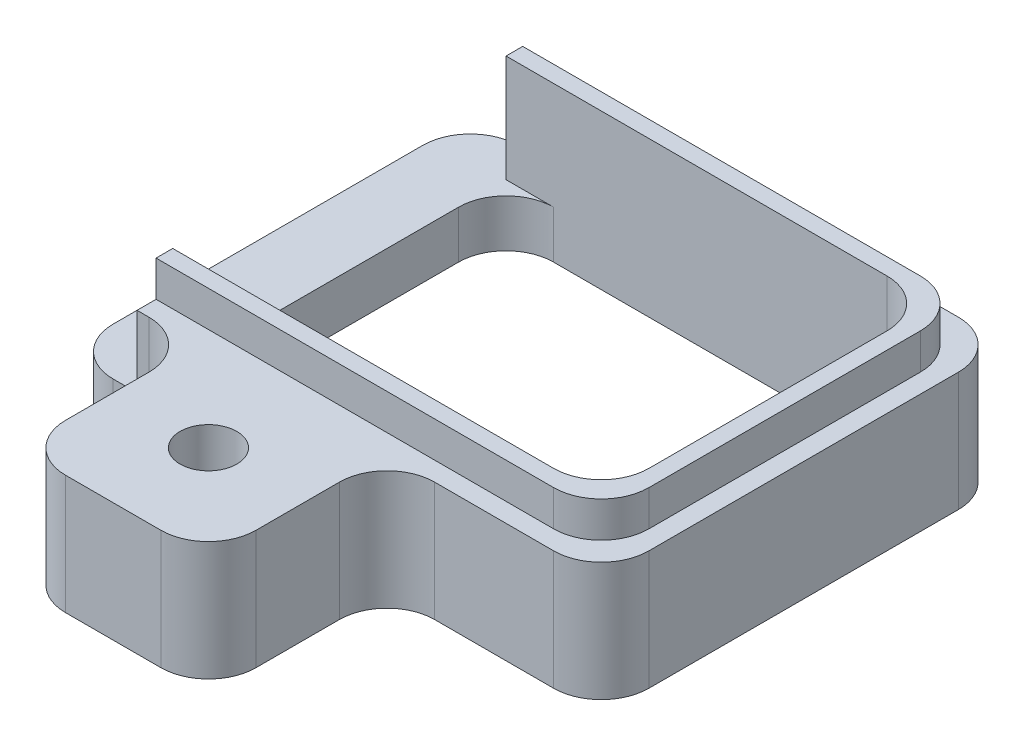
SolidWorks part; units mm, degrees
ref_plane "Front Plane" through (0, 0, 0) normal (0, 0, 1) x (1, 0, 0)
ref_plane "Top Plane" through (0, 0, 0) normal (0, 1, 0) x (1, 0, 0)
ref_plane "Right Plane" through (0, 0, 0) normal (1, 0, 0) x (0, 0, -1)
sketch "Sketch5" plane through (0, 0, 0) normal (0, 1, 0) x (1, 0, 0)
  line L1 (-5.625, -4.25) -> (5.625, -4.25)
  line L2 (-5.625, -4.25) -> (-5.625, 4.25)
  line L3 (-5.625, 4.25) -> (5.625, 4.25)
  line L4 (5.625, -4.25) -> (5.625, 4.25)
  line L5 (-5.625, -4.25) -> (5.625, 4.25) construction
  line L6 (-5.625, 4.25) -> (5.625, -4.25) construction
  point P0 (0, 0)
  dimension "D1" = 8.5
  dimension "D2" = 11.25
extrude "Extrude4" add sketch "Sketch5" along normal blind 2.5
sketch "Sketch19" plane through (0, 2.5, 0) normal (0, 1, 0) x (-1, 0, 0)
  line L0 (5.625, 4.25) -> (-5.625, 4.25) construction
  line L1 (5.625, -4.25) -> (4.125, -4.25)
  line L2 (5.625, -4.25) -> (5.625, 4.25)
  line L3 (5.625, 4.25) -> (4.125, 4.25)
  line L4 (4.125, -4.25) -> (4.125, 4.25)
  dimension "D1" = 1.5
extrude "Extrude12" cut sketch "Sketch19" against normal blind 1.5
sketch "Sketch21" plane through (0, 2.5, 0) normal (0, 1, 0) x (-1, 0, 0)
  line L0 (4.125, 4.25) -> (4.125, -4.25) construction
  line L1 (-4.875, -3.5) -> (4.125, -3.5)
  line L2 (-4.875, -3.5) -> (-4.875, 3.5)
  line L3 (-4.875, 3.5) -> (4.125, 3.5)
  line L4 (4.125, -3.5) -> (4.125, 3.5)
  line L5 (-5.625, -4.25) -> (4.125, -4.25) construction
  line L6 (-5.625, 4.25) -> (-5.625, -4.25) construction
  line L7 (4.125, 4.25) -> (-5.625, 4.25) construction
  dimension "D1" = 0.75
  dimension "D2" = 0.75
  dimension "D3" = 0.75
extrude "Extrude13" cut sketch "Sketch21" against normal through all
sketch "Sketch22" plane through (0, 0, 4.25) normal (0, 0, 1) x (1, 0, 0)
  line L0 (-4.125, 2.5) -> (5.625, 2.5) construction
  line L1 (-2.875, 2.5) -> (1.125, 2.5)
  line L2 (-2.875, 2.5) -> (-2.875, 0)
  line L3 (-2.875, 0) -> (1.125, 0)
  line L4 (1.125, 2.5) -> (1.125, 0)
  line L5 (5.625, 2.5) -> (5.625, 0) construction
  line L6 (-5.625, 0) -> (5.625, 0) construction
  point P8 (0, 0)
  dimension "D1" = 4
  dimension "D2" = 4.5
  dimension "D3" = 0
extrude "Extrude14" add sketch "Sketch22" along normal blind 3.75
sketch "Sketch24" plane through (0, 2.5, 0) normal (0, 1, 0) x (1, 0, 0)
  line L0 (-4.125, 3.85) -> (-4.125, 3.5)
  line L1 (-4.125, 3.5) -> (4.875, 3.5)
  line L2 (4.875, 3.5) -> (4.875, -3.5)
  line L3 (4.875, -3.5) -> (-4.125, -3.5)
  line L4 (-4.125, -3.5) -> (-4.125, -3.85)
  line L9 (-4.125, -3.85) -> (5.225, -3.85)
  line L10 (5.225, -3.85) -> (5.225, 3.85)
  line L11 (5.225, 3.85) -> (-4.125, 3.85)
  line L12 (-4.125, -3.85) -> (5.225, -3.85)
  line L13 (5.225, -3.85) -> (5.225, 3.85)
  line L14 (5.225, 3.85) -> (-4.125, 3.85)
  dimension "D1" = 0.35
extrude "Extrude15" add sketch "Sketch24" along normal blind 0.75
hole_wizard "#0-80 Tapped Hole1" positions "3DSketch1" profile "Sketch26" tap size "#0-80" standard "Ansi Inch"
sketch3d "3DSketch1"
  line L2 (1.125, 2.5, 8) -> (-2.875, 2.5, 8) construction
  line L3 (1.125, 2.5, 8) -> (1.125, 2.5, 4.25) construction
  point P0 (-0.875, 2.5, 6)
  dimension "D1" = 2
  dimension "D2" = 2
sketch "Sketch26" plane through (-0.875, 2.5, 6) normal (1, 0, 0) x (0, 0, 1)
  line L0 (0, 0) -> (0, 79.3679)
  line L1 (0, 79.3679) -> (0.5956, 79.01)
  line L2 (0.5956, 79.01) -> (0.5956, 0)
  line L5 (0.5956, 0) -> (0, 0)
  line L10 (0, 79.3679) -> (-0.5956, 79.01) construction
  line L11 (0, -6.35) -> (0, 107.95) construction
  dimension "Tap Drill Dia." = 1.1913
  dimension "Tap Drill Depth" = 79.01
  dimension "Drill Angle" = 118
fillet "Fillet4" radius 1 14 edges at (5.625, 1.25, -4.25) (5.225, 2.875, -3.85) (5.625, 1.25, 4.25) (5.225, 2.875, 3.85) (4.875, 1.625, 3.5) (4.875, 1.625, -3.5) (-4.125, 0.5, 3.5) (-4.125, 0.5, -3.5) (-5.625, 0.5, -4.25) (-5.625, 0.5, 4.25) (-2.875, 1.25, 8) (1.125, 1.25, 8)
